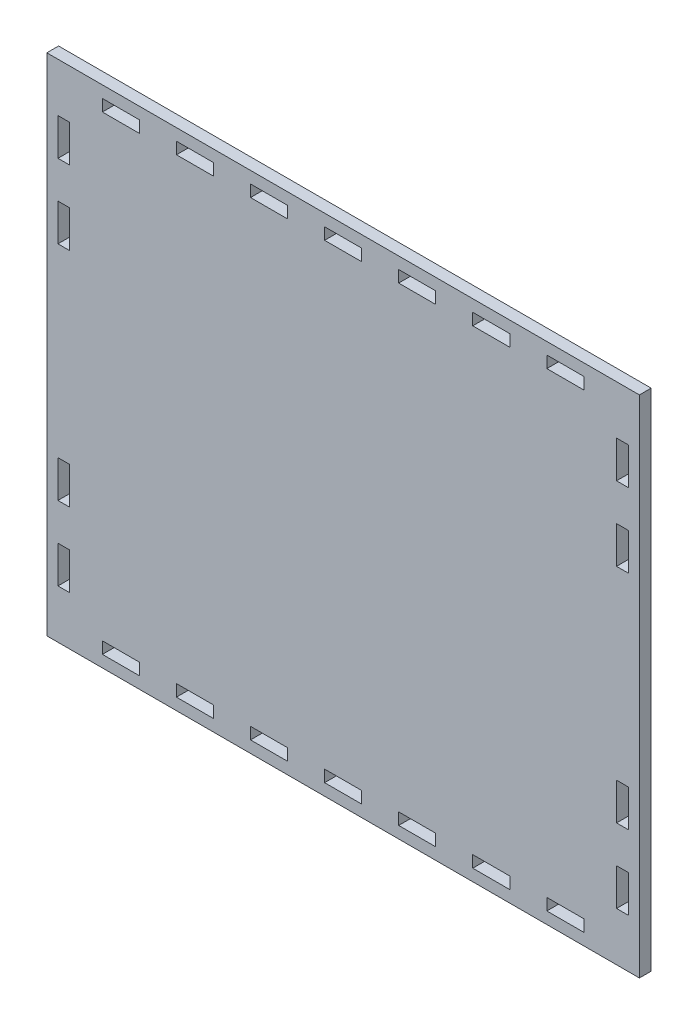
SolidWorks part; units mm, degrees
ref_plane "Front Plane" through (0, 0, 0) normal (0, 0, 1) x (1, 0, 0)
ref_plane "Top Plane" through (0, 0, 0) normal (0, 1, 0) x (1, 0, 0)
ref_plane "Right Plane" through (0, 0, 0) normal (1, 0, 0) x (0, 0, -1)
sketch "Sketch1" plane through (0, 0, 0) normal (0, 0, 1) x (1, 0, 0)
  line L0 (35, 133.07) -> (45, 133.07)
  line L1 (0, -0.105) -> (160, -0.105)
  line L2 (0, -0.105) -> (0, 136.245)
  line L3 (0, 136.245) -> (160, 136.245)
  line L4 (160, -0.105) -> (160, 136.245)
  line L5 (15, 133.07) -> (25, 133.07)
  line L6 (15, 133.07) -> (15, 129.895)
  line L7 (15, 129.895) -> (25, 129.895)
  line L8 (25, 133.07) -> (25, 129.895)
  line L9 (35, 133.07) -> (35, 129.895)
  line L10 (35, 129.895) -> (45, 129.895)
  line L11 (45, 133.07) -> (45, 129.895)
  line L12 (55, 133.07) -> (65, 133.07)
  line L13 (55, 133.07) -> (55, 129.895)
  line L14 (55, 129.895) -> (65, 129.895)
  line L15 (65, 133.07) -> (65, 129.895)
  line L16 (75, 133.07) -> (85, 133.07)
  line L17 (75, 133.07) -> (75, 129.895)
  line L18 (75, 129.895) -> (85, 129.895)
  line L19 (85, 133.07) -> (85, 129.895)
  line L20 (95, 133.07) -> (105, 133.07)
  line L21 (95, 133.07) -> (95, 129.895)
  line L22 (95, 129.895) -> (105, 129.895)
  line L23 (105, 133.07) -> (105, 129.895)
  line L24 (115, 133.07) -> (125, 133.07)
  line L25 (115, 133.07) -> (115, 129.895)
  line L26 (115, 129.895) -> (125, 129.895)
  line L27 (125, 133.07) -> (125, 129.895)
  line L28 (135, 133.07) -> (145, 133.07)
  line L29 (135, 133.07) -> (135, 129.895)
  line L30 (135, 129.895) -> (145, 129.895)
  line L31 (145, 133.07) -> (145, 129.895)
  line L32 (0, 68.07) -> (152.2847, 68.07) construction
  line L33 (145, 3.07) -> (145, 6.245)
  line L34 (135, 6.245) -> (145, 6.245)
  line L35 (135, 3.07) -> (135, 6.245)
  line L36 (135, 3.07) -> (145, 3.07)
  line L37 (125, 3.07) -> (125, 6.245)
  line L38 (115, 6.245) -> (125, 6.245)
  line L39 (115, 3.07) -> (115, 6.245)
  line L40 (115, 3.07) -> (125, 3.07)
  line L41 (105, 3.07) -> (105, 6.245)
  line L42 (95, 6.245) -> (105, 6.245)
  line L43 (95, 3.07) -> (95, 6.245)
  line L44 (95, 3.07) -> (105, 3.07)
  line L45 (85, 3.07) -> (85, 6.245)
  line L46 (75, 6.245) -> (85, 6.245)
  line L47 (75, 3.07) -> (75, 6.245)
  line L48 (75, 3.07) -> (85, 3.07)
  line L49 (65, 3.07) -> (65, 6.245)
  line L50 (55, 6.245) -> (65, 6.245)
  line L51 (55, 3.07) -> (55, 6.245)
  line L52 (55, 3.07) -> (65, 3.07)
  line L53 (45, 3.07) -> (45, 6.245)
  line L54 (35, 6.245) -> (45, 6.245)
  line L55 (35, 3.07) -> (35, 6.245)
  line L56 (25, 3.07) -> (25, 6.245)
  line L57 (15, 6.245) -> (25, 6.245)
  line L58 (15, 3.07) -> (15, 6.245)
  line L59 (15, 3.07) -> (25, 3.07)
  line L60 (35, 3.07) -> (45, 3.07)
  line L61 (3, 43.07) -> (6.175, 43.07)
  line L62 (3, 103.07) -> (6.175, 103.07)
  line L63 (3, 123.07) -> (6.175, 123.07)
  line L64 (3, 123.07) -> (3, 113.07)
  line L65 (3, 113.07) -> (6.175, 113.07)
  line L66 (6.175, 123.07) -> (6.175, 113.07)
  line L67 (3, 103.07) -> (3, 93.07)
  line L68 (3, 93.07) -> (6.175, 93.07)
  line L69 (6.175, 103.07) -> (6.175, 93.07)
  line L70 (3, 43.07) -> (3, 33.07)
  line L71 (3, 33.07) -> (6.175, 33.07)
  line L72 (6.175, 43.07) -> (6.175, 33.07)
  line L73 (3, 23.07) -> (6.175, 23.07)
  line L74 (3, 23.07) -> (3, 13.07)
  line L75 (3, 13.07) -> (6.175, 13.07)
  line L76 (6.175, 23.07) -> (6.175, 13.07)
  line L77 (160, 136.245) -> (0, -0.105) construction
  line L78 (80, 67.5) -> (80, 90.9813) construction
  line L79 (153.825, 23.07) -> (153.825, 13.07)
  line L80 (157, 13.07) -> (153.825, 13.07)
  line L81 (157, 23.07) -> (157, 13.07)
  line L82 (157, 23.07) -> (153.825, 23.07)
  line L83 (153.825, 43.07) -> (153.825, 33.07)
  line L84 (157, 33.07) -> (153.825, 33.07)
  line L85 (157, 43.07) -> (157, 33.07)
  line L86 (157, 43.07) -> (153.825, 43.07)
  line L87 (153.825, 103.07) -> (153.825, 93.07)
  line L88 (157, 93.07) -> (153.825, 93.07)
  line L89 (157, 103.07) -> (157, 93.07)
  line L90 (153.825, 123.07) -> (153.825, 113.07)
  line L91 (157, 113.07) -> (153.825, 113.07)
  line L92 (157, 123.07) -> (157, 113.07)
  line L93 (157, 123.07) -> (153.825, 123.07)
  line L94 (157, 103.07) -> (153.825, 103.07)
  dimension "D1" = 136.35
  dimension "D2" = 160
  dimension "D3" = 10
  dimension "D4" = 3.175
  dimension "D5" = 3.175
  dimension "D7" = 7
  dimension "D8" = 15
  dimension "D6" = 15
  dimension "D9" = 3.175
  dimension "D10" = 3
  dimension "D11" = 10
  dimension "D12" = 13.175
  dimension "D13" = 3.175
  dimension "D14" = 10
  dimension "D15" = 3
  dimension "D16" = 10
  dimension "D17" = 50
  dimension "D18" = 3
  dimension "D19" = 3.175
  dimension "D20" = 3
  dimension "D21" = 10
  dimension "D22" = 3.175
  dimension "D23" = 10
  dimension "D24" = 10
  dimension "D25" = 10
extrude "Boss-Extrude1" add sketch "Sketch1" along normal blind 3.175
